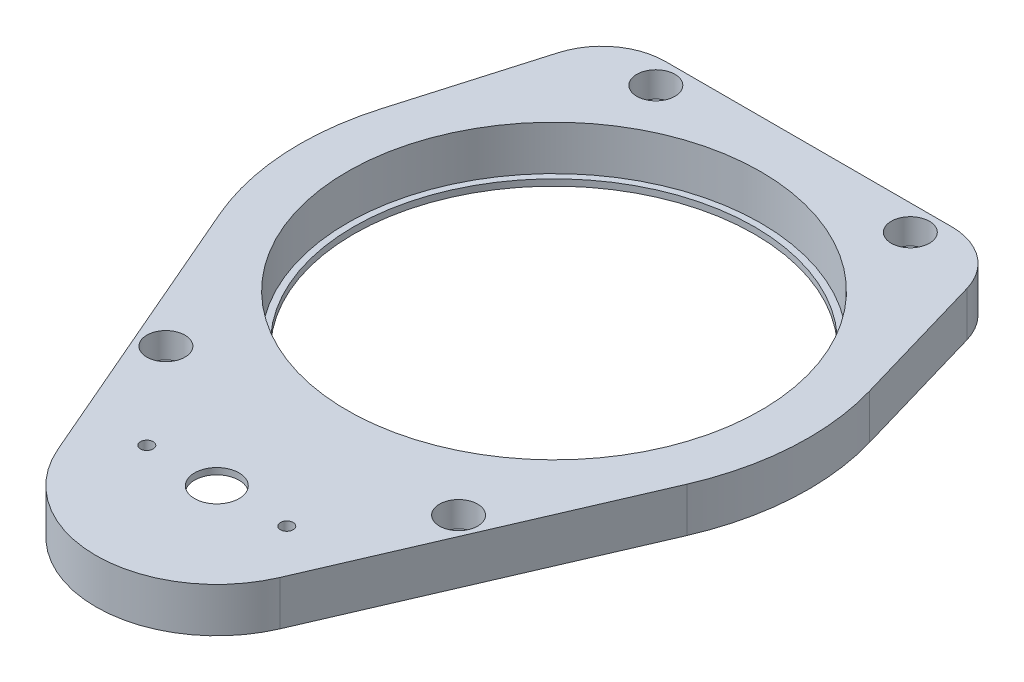
SolidWorks part; units mm, degrees
material "PET"
ref_plane "Front Plane" through (0, 0, 0) normal (0, 0, 1) x (1, 0, 0)
ref_plane "Top Plane" through (0, 0, 0) normal (0, 1, 0) x (1, 0, 0)
ref_plane "Right Plane" through (0, 0, 0) normal (1, 0, 0) x (0, 0, -1)
sketch "Sketch1" plane through (0, 37.073, 0) normal (0, -1, 0) x (1, 0, 0)
  line L0 (-36.7261, 15.8491) -> (-17.4449, 60.5283)
  line L1 (0, 0) -> (0, 53) construction
  line L2 (36.7261, 15.8491) -> (17.4449, 60.5283)
  line L3 (38.4, -11.2) -> (30, -40)
  line L4 (30, -40) -> (-30, -40)
  line L5 (-38.4, -11.2) -> (-30, -40)
  circle A1 centre (0, 53) radius 19
  circle A2 centre (0, 0) radius 40
  circle A3 centre (0, 0) radius 40
  circle A4 centre (0, 0) radius 32.5
  point P14 (0, -40)
  dimension "D3" = 38
  dimension "D4" = 65
  dimension "D2" = 53
  dimension "D5" = 30
  dimension "D1" = 5
extrude "Boss-Extrude1" add sketch "Sketch1" against normal blind 7
sketch "Sketch2" plane through (0, 44.073, 0) normal (0, 1, 0) x (1, 0, 0)
  line L0 (-11, -53) -> (0, -53) construction
  line L1 (0, -53) -> (11, -53) construction
  circle A2 centre (0, -53) radius 3.5
  arc A3 (-17.4449, -60.5283) -> (17.4449, -60.5283) centre (0, -53) ccw
  arc A4 (-17.4449, -60.5283) -> (17.4449, -60.5283) centre (0, -53) ccw
  circle A5 centre (11, -53) radius 1
  circle A6 centre (-11, -53) radius 1
  dimension "D2" = 7
  dimension "D3" = 22
  dimension "D5" = 2
  dimension "D6" = 2
  dimension "D4" = 11
  dimension "D1" = 0
extrude "Cut-Extrude1" cut sketch "Sketch2" against normal blind 10 contours A2 | A5 | A6
sketch "Sketch3" plane through (0, 37.073, 0) normal (0, -1, 0) x (1, 0, 0)
  line L4 (34.8898, 15.0566) -> (15.6086, 59.7358)
  line L5 (-15.6086, 59.7358) -> (-34.8898, 15.0566)
  line L6 (34.8898, 15.0566) -> (15.6086, 59.7358)
  line L7 (-15.6086, 59.7358) -> (-34.8898, 15.0566)
  line L9 (-36.48, -10.64) -> (-28.5, -38)
  line L10 (-36.48, -10.64) -> (-28.5, -38)
  line L11 (-28.5, -38) -> (28.5, -38)
  line L12 (-28.5, -38) -> (28.5, -38)
  line L13 (28.5, -38) -> (36.48, -10.64)
  line L14 (28.5, -38) -> (36.48, -10.64)
  arc A3 (36.48, -10.64) -> (34.8898, 15.0566) centre (0, 0) ccw
  arc A4 (15.6086, 59.7358) -> (-15.6086, 59.7358) centre (0, 53) ccw
  arc A5 (-34.8898, 15.0566) -> (-36.48, -10.64) centre (0, 0) ccw
  arc A6 (15.6086, 59.7358) -> (-15.6086, 59.7358) centre (0, 53) ccw
  arc A7 (-34.8898, 15.0566) -> (-36.48, -10.64) centre (0, 0) ccw
  arc A8 (35.5, 0) -> (35.5, 0) centre (0, 0) ccw
  circle A9 centre (0, 0) radius 35.5
  arc A10 (36.48, -10.64) -> (34.8898, 15.0566) centre (0, 0) ccw
  circle M6 centre (-11, 53) radius 1
  circle M7 centre (11, 53) radius 1
  circle M8 centre (0, 53) radius 3.5
  dimension "D1" = 2
  dimension "D2" = 3
extrude "Cut-Extrude2" cut sketch "Sketch3" against normal blind 6 contours A9 L6 A6 L7 M6 M8 M7
fillet "Fillet1" radius 10 4 edges at (30, 40.573, -40) (-30, 40.573, -40) (28.5, 40.073, -38) (-28.5, 40.073, -38)
sketch "Sketch4" plane through (0, 44.073, 0) normal (0, 1, 0) x (1, 0, 0)
  circle A3 centre (-20, 36) radius 1.5
  circle A6 centre (20, 36) radius 1.5
  circle A9 centre (23, -38) radius 1.5
  circle A12 centre (-23, -38) radius 1.5
extrude "Cut-Extrude3" cut sketch "Sketch4" against normal blind 10
sketch "Sketch5" plane through (0, 43.073, 0) normal (0, -1, 0) x (1, 0, 0)
  circle A2 centre (-23, 38) radius 3.5
  circle A3 centre (-23, 38) radius 3.5
  circle A5 centre (23, 38) radius 3.5
  circle A6 centre (23, 38) radius 3.5
  circle A8 centre (-20, -36) radius 3.5
  circle A9 centre (-20, -36) radius 3.5
  circle A11 centre (20, -36) radius 3.5
  circle A12 centre (20, -36) radius 3.5
  circle A14 centre (-23, 38) radius 1.5
  circle A15 centre (-23, 38) radius 1.5
  circle A17 centre (23, 38) radius 1.5
  circle A18 centre (23, 38) radius 1.5
  circle A20 centre (20, -36) radius 1.5
  circle A21 centre (20, -36) radius 1.5
  circle A23 centre (-20, -36) radius 1.5
  circle A24 centre (-20, -36) radius 1.5
  dimension "D1" = 2
  dimension "D2" = 2
  dimension "D3" = 2
  dimension "D4" = 2
  dimension "D5" = 0
  dimension "D6" = 0
  dimension "D7" = 0
  dimension "D8" = 0
extrude "Boss-Extrude2" add sketch "Sketch5" along normal blind 6
sketch "Sketch6" plane through (0, 44.073, 0) normal (0, 1, 0) x (1, 0, 0)
  circle A2 centre (-20, 36) radius 3
  circle A3 centre (-20, 36) radius 3
  circle A5 centre (20, 36) radius 3
  circle A6 centre (20, 36) radius 3
  circle A8 centre (-23, -38) radius 3
  circle A9 centre (-23, -38) radius 3
  circle A11 centre (23, -38) radius 3
  circle A12 centre (23, -38) radius 3
  dimension "D1" = 1.5
  dimension "D2" = 1.5
  dimension "D3" = 1.5
  dimension "D4" = 1.5
extrude "Cut-Extrude4" cut sketch "Sketch6" against normal blind 4
sketch "Sketch8" plane through (0, 43.073, 0) normal (0, -1, 0) x (1, 0, 0)
  circle A2 centre (-11, 53) radius 1
  circle A3 centre (-11, 53) radius 1
  circle A4 centre (11, 53) radius 3
  circle A5 centre (11, 53) radius 1
  circle A6 centre (11, 53) radius 1
  circle A7 centre (-11, 53) radius 3
  dimension "D1" = 0
  dimension "D2" = 0
  dimension "D3" = 2
  dimension "D4" = 2
extrude "Boss-Extrude3" add sketch "Sketch8" along normal blind 3
sketch "Sketch9" plane through (0, 37.073, 0) normal (0, -1, 0) x (1, 0, 0)
  circle A2 centre (0, 0) radius 35.5
  circle A3 centre (0, 0) radius 35.5
  circle A5 centre (0, 0) radius 31.5
  circle A6 centre (0, 0) radius 31.5
  dimension "D1" = 0
  dimension "D2" = 1
extrude "Boss-Extrude4" add sketch "Sketch9" along normal blind 1
